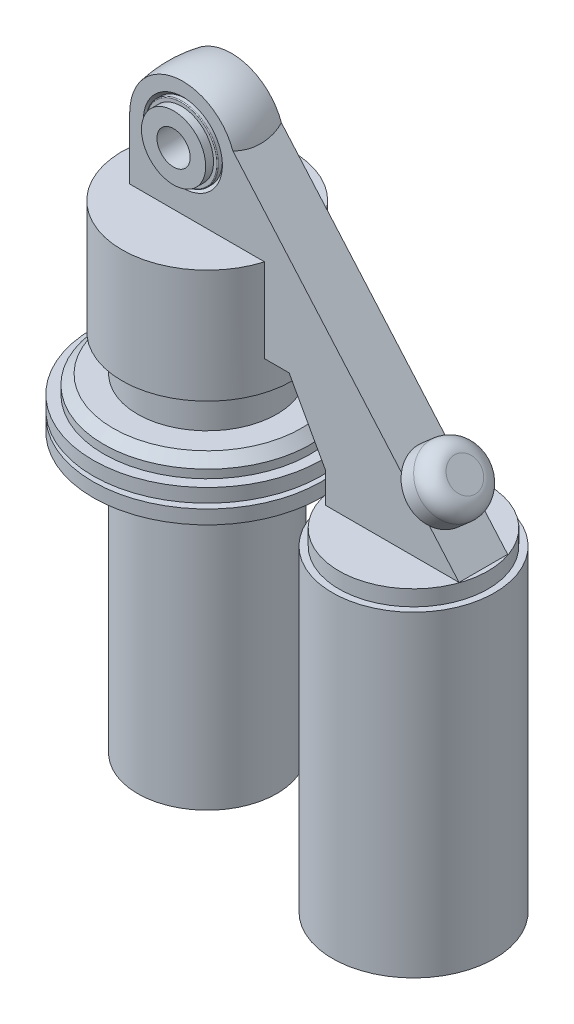
SolidWorks part; units mm, degrees
ref_plane "Front Plane" through (0, 0, 0) normal (0, 0, 1) x (1, 0, 0)
ref_plane "Top Plane" through (0, 0, 0) normal (0, 1, 0) x (1, 0, 0)
ref_plane "Right Plane" through (0, 0, 0) normal (1, 0, 0) x (0, 0, -1)
sketch "Sketch1" plane through (0, 0, 0) normal (0, 1, 0) x (1, 0, 0)
  line L0 (5, 10.0885) -> (5, -10.1115)
  line L1 (5, 10.0885) -> (9.65, 10.0885)
  line L2 (9.65, 10.0885) -> (9.65, 7.7207)
  line L3 (9.65, 7.7207) -> (10.6235, 7.7207)
  line L4 (10.8735, 7.4707) -> (10.8735, 6.3045)
  line L5 (11.8658, 7.2885) -> (10.8735, 6.3045)
  line L6 (0, 9.2654) -> (0, -9.2654) construction
  line L7 (-21.8629, -0.0115) -> (7.8575, -0.0115) construction
  line L8 (11.8658, 7.2885) -> (15.9282, 7.2885)
  line L9 (11.8658, -7.3115) -> (15.9282, -7.3115)
  line L10 (11.8658, -7.3115) -> (10.8735, -6.3275)
  line L11 (10.8735, -7.4937) -> (10.8735, -6.3275)
  line L12 (9.65, -7.7437) -> (10.6235, -7.7437)
  line L13 (9.65, -10.1115) -> (9.65, -7.7437)
  line L14 (5, -10.1115) -> (9.65, -10.1115)
  line L15 (9.65, 7.7207) -> (9.65, -0.0115) construction
  line L16 (9.65, -0.0115) -> (9.65, -7.7437) construction
  arc A0 (15.9282, 7.2885) -> (15.9282, -7.3115) centre (-23.4, -0.0115) cw
  arc A1 (10.8735, -7.4937) -> (10.6235, -7.7437) centre (10.6235, -7.4937) cw
  arc A2 (10.6235, 7.7207) -> (10.8735, 7.4707) centre (10.6235, 7.4707) cw
  point P2 (-4.3463, -0.0115)
  point P18 (16.6, -0.0115)
  point P20 (5, -0.0115)
  dimension "D5" = 0.25
  dimension "D6" = 16.6
  dimension "D7" = 40
  dimension "D1" = 20.2
  dimension "D2" = 10
  dimension "D3" = 19.3
  dimension "D4" = 14.6
revolve "Revolve1" add sketch "Sketch1"
sketch "Sketch2" plane through (0, 0, 0) normal (0, 0, 1) x (1, 0, 0)
  line L1 (0, 42.6805) -> (0, -22.2739) construction
  line L9 (-15, 0) -> (-16, 0)
  line L10 (-16, -44) -> (-16, 0)
  line L11 (-0.0718, -44) -> (-16, -44)
  line L12 (31.9282, -44) -> (-0.0718, -44)
  line L13 (42.9282, -64) -> (31.9282, -44)
  line L14 (42.9282, -73) -> (42.9282, -64)
  line L15 (83, -73) -> (42.9282, -73)
  line L16 (12.6886, 8) -> (83, -73)
  arc A4 (12.6886, 8) -> (-15, 0) centre (0, 0) cw
  dimension "D1" = 83
  dimension "D5" = 15
  dimension "D2" = 73
  dimension "D3" = 16
  dimension "D4" = 8
extrude "Extrude1" add sketch "Sketch2" along normal up to surface and the other way up to surface up to face at (-15.9282, 0, 7.3115) other way up to face at (-11.8658, 0, -7.2885)
sketch "Sketch5" plane through (0, 0, 0) normal (0, 0, 1) x (1, 0, 0)
  line L0 (-25.6, -18.8) -> (-25.6, -52.9)
  line L1 (-34.3, -69.2) -> (-31.1, -69.2)
  line L2 (0, 0) -> (0, -216.0086) construction
  line L3 (-25.6, -52.9) -> (-20.95, -52.9)
  line L4 (-20.95, -52.9) -> (-20.95, -63.9)
  line L5 (-31.1, -69.2) -> (-31.1, -66.7)
  line L6 (-34.3, -69.2) -> (-34.3, -73.3)
  line L7 (-34.3, -73.3) -> (-30.4, -73.3)
  line L8 (-20.95, -78.95) -> (-20.95, -162.65)
  line L9 (-20.95, -162.65) -> (0, -162.65)
  line L10 (0, -162.65) -> (0, -18.8)
  line L11 (-30.4, -73.3) -> (-30.4, -74.8)
  line L12 (-30.4, -74.8) -> (-34.3, -74.8)
  line L13 (-34.3, -74.8) -> (-34.3, -78.95)
  line L14 (-34.3, -78.95) -> (-20.95, -78.95)
  line L15 (-31.1, -66.7) -> (-28.3, -63.9)
  line L16 (-28.3, -63.9) -> (-20.95, -63.9)
  line L17 (-31.1, -66.7) -> (-15.7575, -66.7) construction
  line L18 (-25.6, -18.8) -> (0, -18.8)
  dimension "D1" = 34.3
  dimension "D2" = 15.05
  dimension "D3" = 18.8
  dimension "D4" = 25.6
  dimension "D5" = 11
  dimension "D6" = 78.95
  dimension "D7" = 4.15
  dimension "D8" = 1.5
  dimension "D9" = 4.1
  dimension "D10" = 2.5
  dimension "D11" = 62.2
  dimension "D12" = 60.8
  dimension "D13" = 83.7
  dimension "D14" = 41.9
  dimension "D15" = 45
revolve "Revolve2" add sketch "Sketch5" angle 360 about L2
sketch3d "3DSketch1"
  line L0 (0, -162.65, 0) -> (0, 22.4913, 0) construction
  line L1 (0, -162.65, 0) -> (0, -78.95, 0) construction
  line L2 (0, 0, 10.0885) -> (0, 0, -10.0885) construction
  line L3 (0, 0, 10.1115) -> (0, 0, -10.0885) construction
  line L4 (0, 0, 10.1115) -> (0, 0, 7.7437) construction
  point P10 (0, 0, 0)
sketch "Sketch6" plane through (0, 0, 0) normal (0, 0, 1) x (1, 0, 0)
  line L0 (62, -208.5399) -> (62, -21.7963) construction
  line L1 (86.35, -172.9) -> (86.35, -77.7)
  line L2 (86.35, -172.9) -> (84.3657, -172.9)
  line L3 (83.0117, -172.3094) -> (84.3657, -171.3768)
  line L4 (86.35, -77.7) -> (84.3903, -77.7)
  line L5 (62, -73) -> (62, -178.2241)
  line L6 (84.3903, -77.7) -> (84.3903, -73)
  line L7 (84.3657, -171.3768) -> (84.3657, -172.9)
  line L9 (83.0117, -172.3094) -> (81.1352, -172.3094)
  line L10 (81.1352, -172.3094) -> (79.985, -169.3982)
  line L11 (83, -73) -> (42.9282, -73) construction
  line L12 (79.985, -169.3982) -> (73.1488, -169.3982)
  line L13 (84.3903, -73) -> (62, -73)
  line L14 (73.1488, -169.3982) -> (71.7781, -173.1016)
  line L16 (71.7781, -173.1016) -> (70.3418, -173.1016)
  line L18 (70.3418, -173.1016) -> (70.3418, -176.5493)
  line L20 (70.3418, -176.5493) -> (68.7442, -176.5493)
  line L21 (68.7442, -176.5493) -> (67.4435, -178.2241)
  line L22 (67.4435, -178.2241) -> (62, -178.2241)
  line L23 (0, -162.65) -> (0, 22.4913) construction
  dimension "D1" = 77.7
  dimension "D2" = 95.2
  dimension "D3" = 62
  dimension "D4" = 48.7
revolve "Revolve3" add sketch "Sketch6" angle 360 about L0
ref_plane "Plane1" through (75, 0, 0) normal (1, 0, 0) x (0, 0, -1)
sketch "Sketch9" plane through (33.3518, -15.8044, 0) normal (0.7552, 0.6555, 0) x (0, 0, -1)
  line L0 (-7.3115, -75.7382) -> (7.2885, -75.7382) construction
  circle A0 centre (0, -55.7382) radius 9.73
  dimension "D1" = 20
extrude "Extrude2" add sketch "Sketch9" along normal blind 10
fillet "Fillet1" radius 5 1 edges at (71.063, -43.9934, 0)
